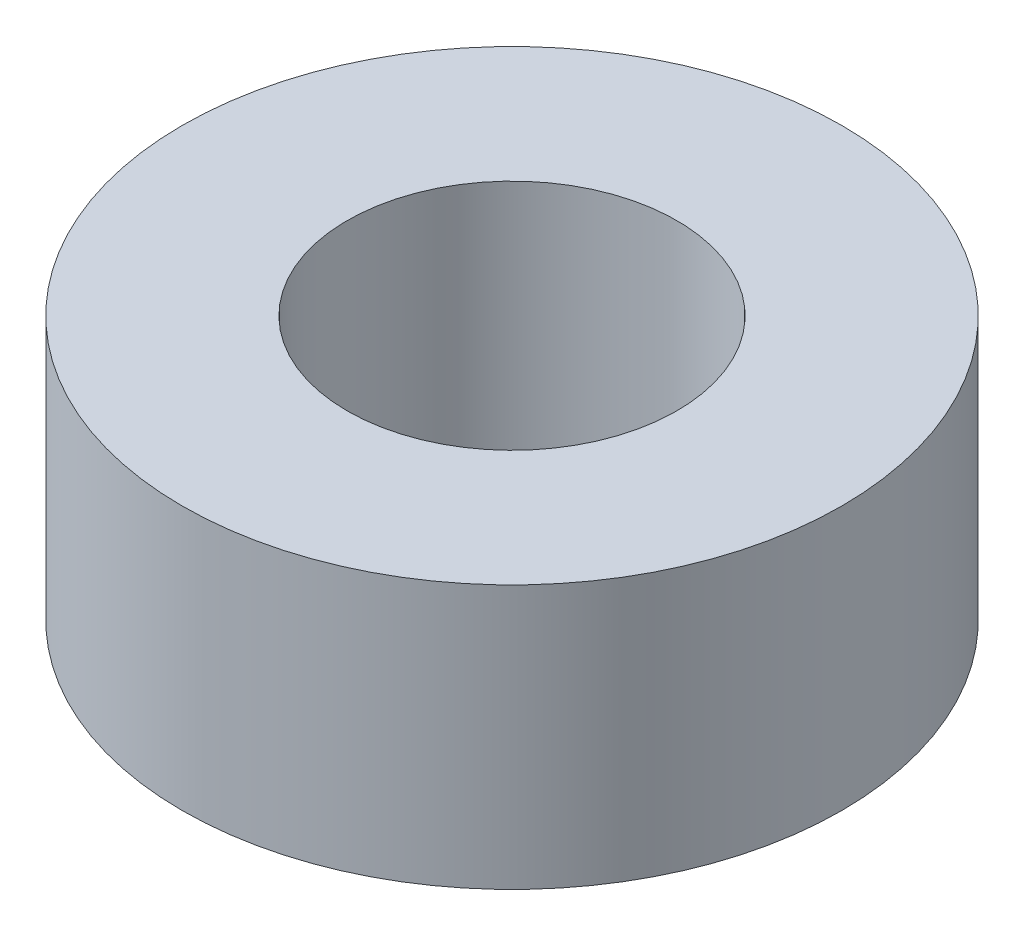
SolidWorks part; units mm, degrees
ref_plane "Front" through (0, 0, 0) normal (0, 0, 1) x (1, 0, 0)
ref_plane "Top" through (0, 0, 0) normal (0, 1, 0) x (1, 0, 0)
ref_plane "Right" through (0, 0, 0) normal (1, 0, 0) x (0, 0, -1)
sketch "Sketch2" plane through (0, 0, 0) normal (0, 1, 0) x (1, 0, 0)
  circle A0 centre (0, 0) radius 2.5
  circle A1 centre (0, 0) radius 5
  dimension "D1" = 10
  dimension "D2" = 5
extrude "Boss-Extrude1" add sketch "Sketch2" along normal blind 4
